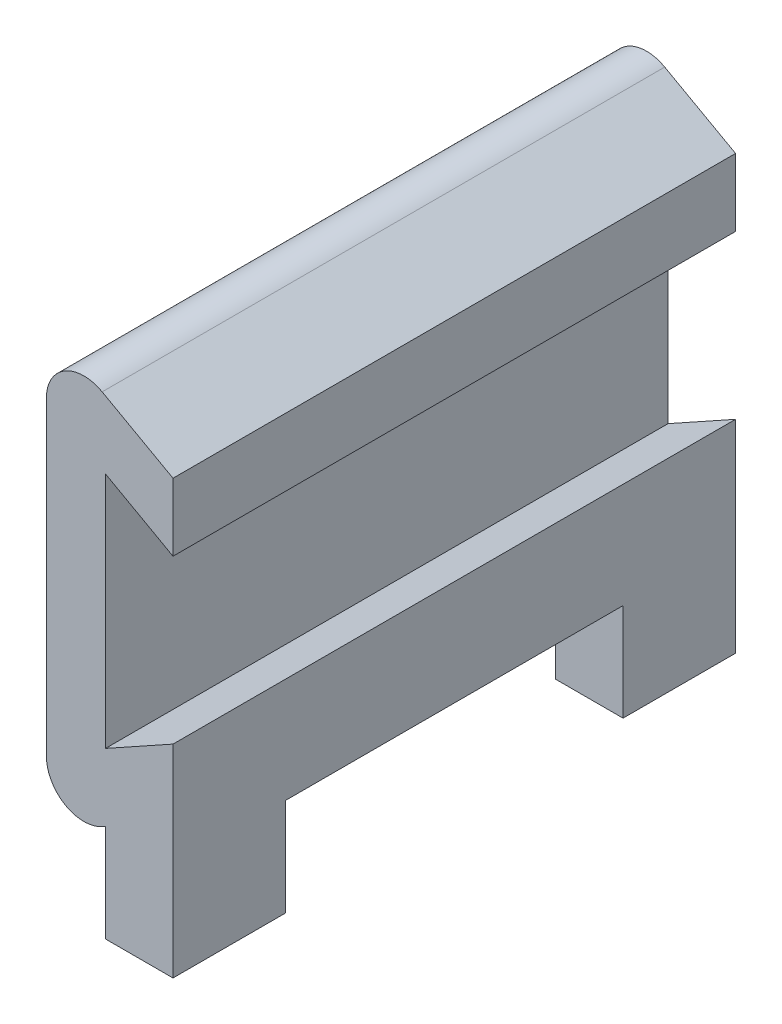
SolidWorks part; units mm, degrees
ref_plane "Front Plane" through (0, 0, 0) normal (0, 0, 1) x (1, 0, 0)
ref_plane "Top Plane" through (0, 0, 0) normal (0, 1, 0) x (1, 0, 0)
ref_plane "Right Plane" through (0, 0, 0) normal (1, 0, 0) x (0, 0, -1)
sketch "Sketch2" plane through (0, 0, 0) normal (0, 0, 1) x (1, 0, 0)
  line L0 (-50.411, 61.1748) -> (-48.125, 59.9048)
  line L4 (-49.911, 53.975) -> (-49.911, 60.325)
  line L6 (-49.911, 60.325) -> (-48.125, 59.3328)
  line L7 (-48.125, 54.9672) -> (-49.911, 53.975)
  line L9 (-50.411, 53.1252) -> (-50.411, 61.1748)
  line L10 (-52.411, 64.5738) -> (-48.125, 62.1927)
  line L12 (-48.125, 52.1073) -> (-52.411, 49.7262)
  line L13 (-52.411, 49.7262) -> (-52.411, 64.5738)
  line L14 (-45.125, 53.774) -> (-45.125, 60.526) construction
  line L15 (-47.125, 54.9508) -> (-47.125, 59.3492) construction
  line L18 (-52.411, 64.5738) -> (-45.125, 60.526) construction
  line L19 (-45.125, 53.774) -> (-52.411, 49.7262) construction
  line L21 (-50.411, 61.1748) -> (-47.125, 59.3492) construction
  line L22 (-48.125, 62.1927) -> (-48.125, 52.1073)
  line L23 (-49.911, 60.325) -> (-47.625, 59.055) construction
  line L24 (-47.625, 55.245) -> (-47.625, 59.055) construction
  line L25 (-47.625, 55.245) -> (-49.911, 53.975) construction
  line L26 (-48.125, 54.3952) -> (-50.411, 53.1252)
  line L27 (-47.125, 54.9508) -> (-50.411, 53.1252) construction
  point P9 (-47.625, 59.055)
  point P10 (-47.625, 55.245)
  dimension "D1" = 6.35
  dimension "D2" = 1.27
  dimension "D3" = 1.27
  dimension "D5" = 0.5
  dimension "D6" = 2
extrude "Boss-Extrude1" add sketch "Sketch2" along normal blind 19.05 contours L22 L26 L9 L0 L10 L13 L12
fillet "Fillet1" radius 1.27 2 edges at (-52.411, 49.7262, 9.525) (-52.411, 64.5738, 9.525)
sketch "Sketch3" plane through (0, 0, 19.05) normal (0, 0, 1) x (1, 0, 0)
  line L0 (-50.411, 53.1252) -> (-50.411, 61.1748) construction
  line L1 (-48.125, 52.1073) -> (-50.411, 52.1073)
  line L2 (-48.125, 52.1073) -> (-48.125, 47.5353)
  line L3 (-48.125, 47.5353) -> (-50.411, 47.5353)
  line L4 (-50.411, 52.1073) -> (-50.411, 47.5353)
  dimension "D1" = 4.572
extrude "Boss-Extrude2" add sketch "Sketch3" against normal through all
sketch "Sketch4" plane through (-50.411, 0, 0) normal (-1, 0, 0) x (0, 0, 1)
  line L0 (0, 47.5353) -> (19.05, 47.5353) construction
  line L1 (3.81, 50.8373) -> (15.24, 50.8373)
  line L2 (3.81, 50.8373) -> (3.81, 47.5353)
  line L3 (3.81, 47.5353) -> (15.24, 47.5353)
  line L4 (15.24, 50.8373) -> (15.24, 47.5353)
  line L5 (19.05, 50.8373) -> (0, 50.8373) construction
  line L6 (19.05, 50.8373) -> (19.05, 47.5353) construction
  line L7 (0, 50.8373) -> (0, 47.5353) construction
  dimension "D1" = 3.81
  dimension "D2" = 3.81
extrude "Cut-Extrude2" cut sketch "Sketch4" against normal through all
